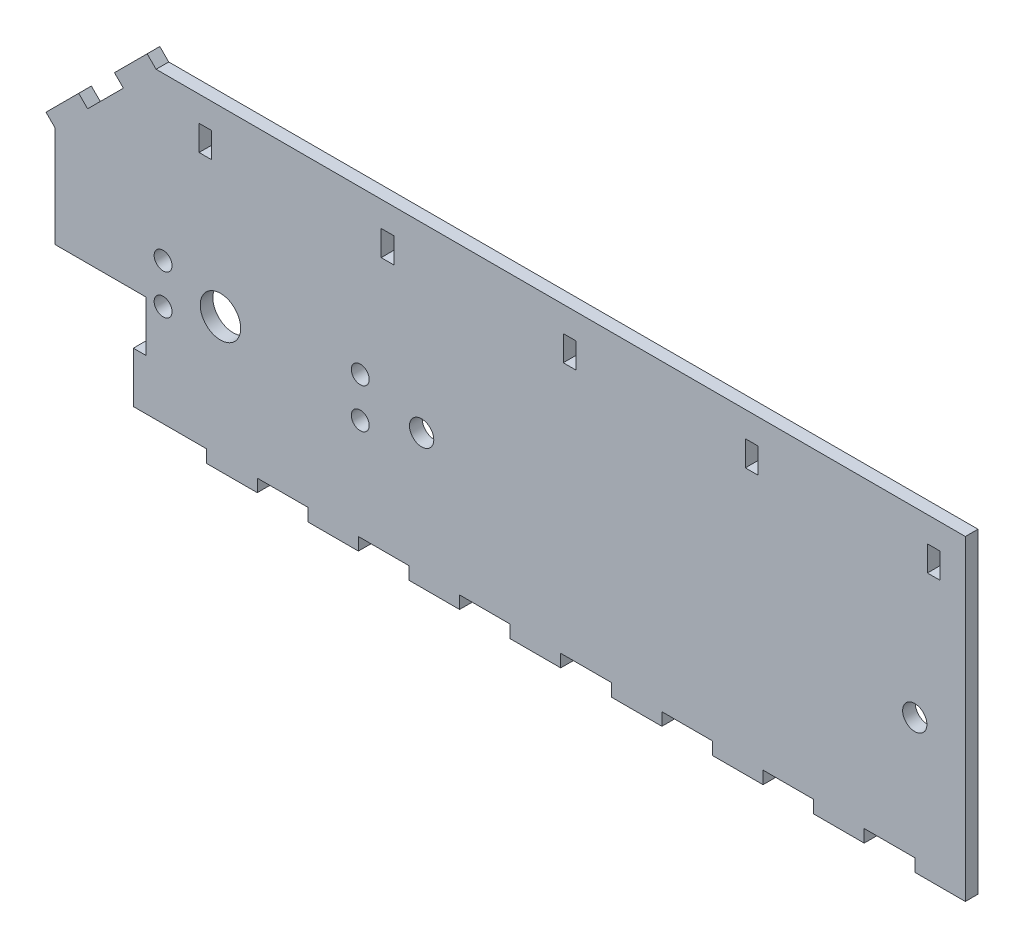
SolidWorks part; units mm, degrees
ref_plane "Front" through (0, 0, 0) normal (0, 0, 1) x (1, 0, 0)
ref_plane "Top" through (0, 0, 0) normal (0, 1, 0) x (1, 0, 0)
ref_plane "Right" through (0, 0, 0) normal (1, 0, 0) x (0, 0, -1)
sketch "Sketch1" plane through (0, 0, 0) normal (0, 0, 1) x (1, 0, 0)
  line L5 (0, 0) -> (228.6, 0)
  line L6 (0, 0) -> (0, 76.2)
  line L7 (0, 76.2) -> (228.6, 76.2)
  line L8 (228.6, 0) -> (228.6, 76.2)
  circle A0 centre (215.9, 30.48) radius 3.048
  circle A1 centre (92.075, 30.48) radius 3.048
  circle A2 centre (41.5608, 30.48) radius 5.08
  dimension "D7" = 6.096
  dimension "D8" = 6.096
  dimension "D9" = 10.16
  dimension "D1" = 228.6
  dimension "D2" = 76.2
  dimension "D3" = 50.5142
  dimension "D4" = 123.825
  dimension "D5" = 30.48
  dimension "D6" = 12.7
extrude "Boss-Extrude1" add sketch "Sketch1" along normal blind 3.175
sketch "Sketch2" plane through (0, 0, 0) normal (0, -1, 0) x (1, 0, 0)
  line L0 (0, 3.175) -> (228.6, 3.175) construction
  line L1 (228.6, 0) -> (215.9, 0)
  line L2 (228.6, 0) -> (228.6, 3.175)
  line L3 (228.6, 3.175) -> (215.9, 3.175)
  line L4 (215.9, 0) -> (215.9, 3.175)
  line L5 (203.2, 0) -> (203.2, 3.175)
  line L6 (203.2, 0) -> (190.5, 0)
  line L7 (190.5, 0) -> (190.5, 3.175)
  line L8 (203.2, 3.175) -> (190.5, 3.175)
  line L9 (177.8, 0) -> (177.8, 3.175)
  line L10 (177.8, 0) -> (165.1, 0)
  line L11 (165.1, 0) -> (165.1, 3.175)
  line L12 (177.8, 3.175) -> (165.1, 3.175)
  line L13 (152.4, 0) -> (152.4, 3.175)
  line L14 (152.4, 0) -> (139.7, 0)
  line L15 (139.7, 0) -> (139.7, 3.175)
  line L16 (152.4, 3.175) -> (139.7, 3.175)
  line L17 (127, 0) -> (127, 3.175)
  line L18 (127, 0) -> (114.3, 0)
  line L19 (114.3, 0) -> (114.3, 3.175)
  line L20 (127, 3.175) -> (114.3, 3.175)
  line L21 (101.6, 0) -> (101.6, 3.175)
  line L22 (101.6, 0) -> (88.9, 0)
  line L23 (88.9, 0) -> (88.9, 3.175)
  line L24 (101.6, 3.175) -> (88.9, 3.175)
  line L25 (76.2, 0) -> (76.2, 3.175)
  line L26 (76.2, 0) -> (63.5, 0)
  line L27 (63.5, 0) -> (63.5, 3.175)
  line L28 (76.2, 3.175) -> (63.5, 3.175)
  line L29 (50.8, 0) -> (50.8, 3.175)
  line L30 (50.8, 0) -> (38.1, 0)
  line L31 (38.1, 0) -> (38.1, 3.175)
  line L32 (50.8, 3.175) -> (38.1, 3.175)
  dimension "D1" = 12.7
  dimension "D2" = 8
extrude "Boss-Extrude2" add sketch "Sketch2" along normal blind 3.175
sketch "Sketch3" plane through (0, 0, 0) normal (0, 0, -1) x (-1, 0, 0)
  line L1 (0, 0) -> (-22.86, 0)
  line L2 (0, 0) -> (0, 25.4)
  line L3 (0, 25.4) -> (-22.86, 25.4)
  line L4 (-22.86, 0) -> (-22.86, 25.4)
  dimension "D1" = 25.4
  dimension "D2" = 22.86
extrude "Cut-Extrude1" cut sketch "Sketch3" against normal through all
sketch "Sketch4" plane through (22.86, 0, 0) normal (-1, 0, 0) x (0, 0, 1)
  line L0 (3.175, 25.4) -> (3.175, 0) construction
  line L1 (0, 0) -> (3.175, 0)
  line L2 (0, 0) -> (0, 12.7)
  line L3 (0, 12.7) -> (3.175, 12.7)
  line L4 (3.175, 0) -> (3.175, 12.7)
  dimension "D1" = 12.7
extrude "Boss-Extrude3" add sketch "Sketch4" along normal blind 3.175
sketch "Sketch6" plane through (0, 0, 0) normal (0, 0, -1) x (-1, 0, 0)
  circle A0 centre (-27.1608, 35.48) radius 2.25
  circle A1 centre (-27.1608, 25.48) radius 2.25
  circle A2 centre (-76.6608, 35.48) radius 2.25
  circle A3 centre (-76.6608, 25.48) radius 2.25
extrude "Cut-Extrude2" cut sketch "Sketch6" against normal through all
sketch "Sketch8" plane through (0, 0, 3.175) normal (0, 0, 1) x (1, 0, 0)
  line L1 (228.6, 76.2) -> (0, 76.2) construction
  line L5 (25.4, 76.2) -> (0, 76.2)
  line L7 (0, 76.2) -> (0, 50.8)
  line L10 (0, 76.2) -> (0, 25.4) construction
  line L11 (0, 50.8) -> (25.4, 76.2)
  dimension "D1" = 45
extrude "Cut-Extrude3" cut sketch "Sketch8" against normal through all
sketch "Sketch12" plane through (0, 0, 0) normal (0, 0, -1) x (-1, 0, 0)
  line L0 (-164.0363, 64) -> (-164.0363, 1) construction
  line L1 (-139.0363, 1) -> (-139.0363, 64) construction
  line L2 (-140.0363, 65) -> (-163.0363, 65) construction
  line L3 (-164.0363, 64) -> (-164.0363, 1) construction
  line L4 (-139.0363, 1) -> (-139.0363, 64) construction
  line L5 (-140.0363, 65) -> (-163.0363, 65) construction
  line L6 (-228.6, 76.2) -> (-25.4, 76.2) construction
  line L7 (-222.25, 69.85) -> (-219.075, 69.85)
  line L8 (-222.25, 69.85) -> (-222.25, 63.5)
  line L9 (-222.25, 63.5) -> (-219.075, 63.5)
  line L10 (-219.075, 69.85) -> (-219.075, 63.5)
  line L11 (-228.6, -3.175) -> (-228.6, 76.2) construction
  line L12 (-176.53, 69.85) -> (-176.53, 63.5)
  line L13 (-176.53, 69.85) -> (-173.355, 69.85)
  line L14 (-173.355, 69.85) -> (-173.355, 63.5)
  line L15 (-176.53, 63.5) -> (-173.355, 63.5)
  line L16 (-130.81, 69.85) -> (-130.81, 63.5)
  line L17 (-130.81, 69.85) -> (-127.635, 69.85)
  line L18 (-127.635, 69.85) -> (-127.635, 63.5)
  line L19 (-130.81, 63.5) -> (-127.635, 63.5)
  line L20 (-85.09, 69.85) -> (-85.09, 63.5)
  line L21 (-85.09, 69.85) -> (-81.915, 69.85)
  line L22 (-81.915, 69.85) -> (-81.915, 63.5)
  line L23 (-85.09, 63.5) -> (-81.915, 63.5)
  line L24 (-39.37, 69.85) -> (-39.37, 63.5)
  line L25 (-39.37, 69.85) -> (-36.195, 69.85)
  line L26 (-36.195, 69.85) -> (-36.195, 63.5)
  line L27 (-39.37, 63.5) -> (-36.195, 63.5)
  dimension "D1" = 6.35
  dimension "D2" = 3.175
  dimension "D3" = 6.35
  dimension "D4" = 6.35
  dimension "D5" = 5
extrude "Cut-Extrude5" cut sketch "Sketch12" against normal blind 3.175
sketch "Sketch13" plane through (-25.4, 25.4, 0) normal (-0.7071, 0.7071, 0) x (0, 0, 1)
  line L0 (0, 35.921) -> (0, 71.842) construction
  line L1 (3.175, 71.842) -> (0, 71.842)
  line L2 (3.175, 71.842) -> (3.175, 60.2315)
  line L3 (3.175, 60.2315) -> (0, 60.2315)
  line L4 (0, 71.842) -> (0, 60.2315)
  line L10 (3.175, 35.921) -> (0, 35.921)
  line L11 (3.175, 35.921) -> (3.175, 47.5315)
  line L12 (3.175, 47.5315) -> (0, 47.5315)
  line L13 (0, 35.921) -> (0, 47.5315)
  dimension "D1" = 12.7
extrude "Boss-Extrude5" add sketch "Sketch13" along normal blind 3.175
